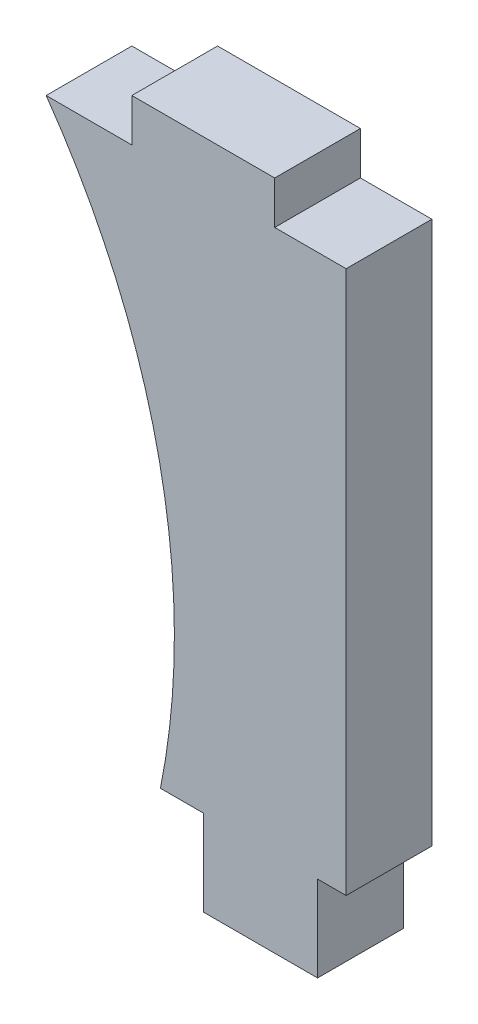
SolidWorks part; units mm, degrees
ref_plane "Alzado" through (0, 0, 0) normal (0, 0, 1) x (1, 0, 0)
ref_plane "Planta" through (0, 0, 0) normal (0, 1, 0) x (1, 0, 0)
ref_plane "Vista lateral" through (0, 0, 0) normal (1, 0, 0) x (0, 0, -1)
sketch "Croquis2" plane through (0, 0, 0) normal (0, 0, 1) x (1, 0, 0)
  line L0 (-1.5, 0) -> (0, 0)
  line L1 (0, 0) -> (0, -3)
  line L2 (0, -3) -> (4, -3)
  line L3 (4, -3) -> (4, 0)
  line L4 (4, 0) -> (5, 0)
  line L5 (5, 0) -> (5, 19)
  line L6 (5, 19) -> (2.5, 19)
  line L7 (2.5, 19) -> (2.5, 20.5)
  line L8 (2.5, 20.5) -> (-2.5, 20.5)
  line L9 (-2.5, 20.5) -> (-2.5, 19)
  line L10 (-2.5, 19) -> (-5.5, 19)
  arc A1 (-5.5, 19) -> (-1.5, 0) centre (-25.5119, 4.8659) cw
  dimension "D9" = 24.5
  dimension "D1" = 3
  dimension "D2" = 4
  dimension "D3" = 19
  dimension "D4" = 1
  dimension "D5" = 1.5
  dimension "D6" = 3
  dimension "D7" = 5
  dimension "D8" = 2.5
  dimension "D10" = 1.5
extrude "Saliente-Extruir1" add sketch "Croquis2" along normal blind 3
